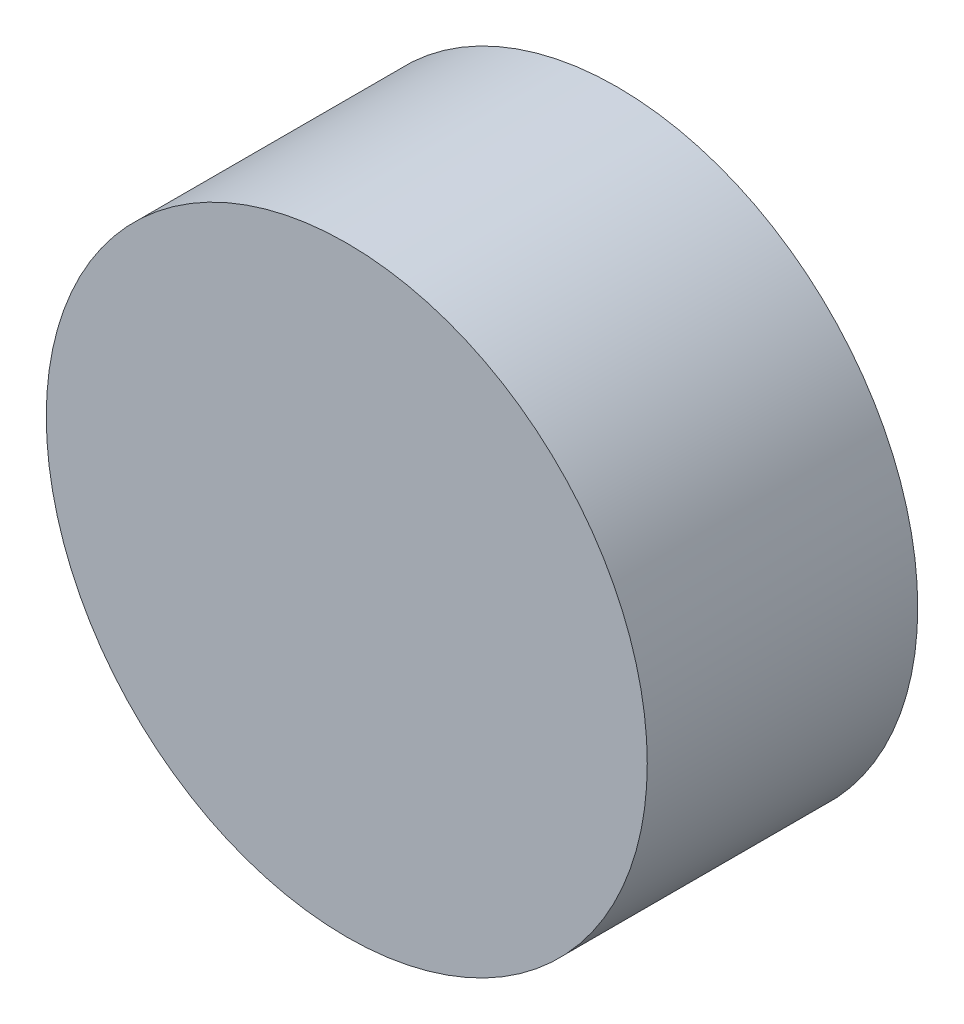
SolidWorks part; units mm, degrees
ref_plane "Front Plane" through (0, 0, 0) normal (0, 0, 1) x (1, 0, 0)
ref_plane "Top Plane" through (0, 0, 0) normal (0, 1, 0) x (1, 0, 0)
ref_plane "Right Plane" through (0, 0, 0) normal (1, 0, 0) x (0, 0, -1)
sketch "Sketch1" plane through (0, 0, 0) normal (0, 0, 1) x (1, 0, 0)
  line L0 (-139.86, -240.082) -> (37.94, -240.082) construction
  line L1 (-25, 142.2564) -> (-25, -171.8) construction
  circle A0 centre (0, -150.082) radius 10
  point P4 (0, 0)
  dimension "D1" = 20
  dimension "D2" = 90
  dimension "D3" = 25
extrude "Boss-Extrude1" add sketch "Sketch1" along normal blind 9
